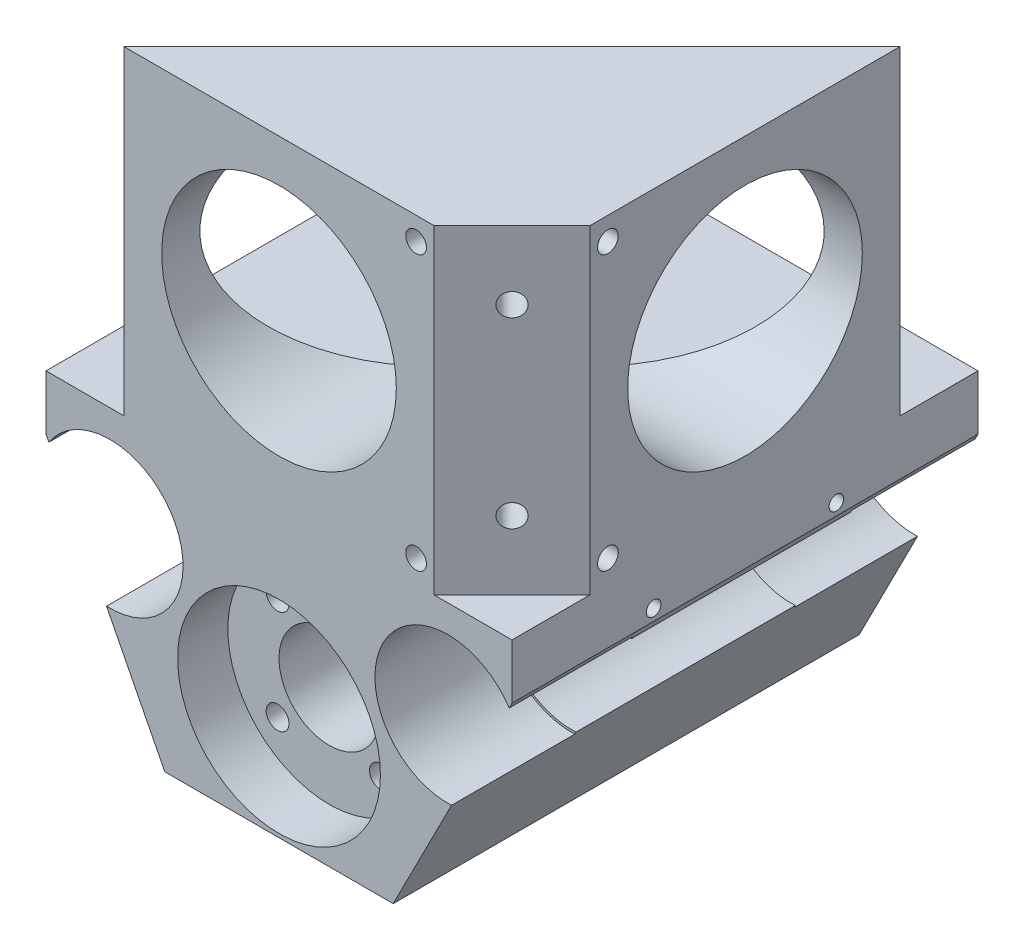
SolidWorks part; units mm, degrees
material "7075-T6 (SN)"
ref_plane "Front Plane" through (0, 0, 0) normal (0, 0, 1) x (1, 0, 0)
ref_plane "Top Plane" through (0, 0, 0) normal (0, 1, 0) x (1, 0, 0)
ref_plane "Right Plane" through (0, 0, 0) normal (1, 0, 0) x (0, 0, -1)
sketch "Sketch1" plane through (0, 0, 0) normal (0, 0, 1) x (1, 0, 0)
  line L0 (-25.5, 0) -> (25.5, 0)
  line L1 (-25.5, 0) -> (-25.5, -6)
  line L2 (-25.5, -6) -> (-12.5, -31.5)
  line L3 (-12.5, -31.5) -> (12.5, -31.5)
  line L4 (12.5, -31.5) -> (25.5, -6)
  line L5 (25.5, -6) -> (25.5, 0)
  point P7 (0, -31.5)
  dimension "D1" = 51
  dimension "D2" = 31.5
  dimension "D3" = 25
  dimension "D4" = 6
extrude "Boss-Extrude1" add sketch "Sketch1" along normal blind 51
sketch "Sketch2" plane through (0, 0, 51) normal (0, 0, 1) x (1, 0, 0)
  line L2 (-18.5, -11) -> (18.5, -11) construction
  line L3 (25.5, 0) -> (-25.5, 0) construction
  circle A2 centre (-18.5, -11) radius 7.75
  circle A3 centre (18.5, -11) radius 7.75
  point P4 (0, -11)
  dimension "D1" = 15.5
  dimension "D2" = 37
  dimension "D3" = 11
extrude "Cut-Extrude1" cut sketch "Sketch2" against normal up to next
sketch "Sketch6" plane through (0, 0, 51) normal (0, 0, 1) x (1, 0, 0)
  line L0 (-12.5, -31.5) -> (12.5, -31.5) construction
  circle A0 centre (0, -20) radius 5.5
  dimension "D1" = 11
  dimension "D2" = 11.5
extrude "Cut-Extrude2" cut sketch "Sketch6" against normal up to next
hole_wizard "M3 Tapped Hole2" positions "Sketch7" profile "Sketch8" tap size "M3" standard "DIN"
sketch "Sketch7" plane through (0, 0, 51) normal (0, 0, 1) x (1, 0, 0)
  line L0 (5.6569, -14.3431) -> (-5.6569, -25.6569) construction
  line L2 (-5.6569, -14.3431) -> (5.6569, -25.6569) construction
  circle A2 centre (0, -20) radius 5.5 construction
  point P0 (-5.6569, -14.3431)
  point P2 (5.6569, -25.6569)
  point P4 (5.6569, -14.3431)
  point P6 (-5.6569, -25.6569)
  point P25 (0, -20)
  point P26 (0, -20)
  dimension "D1" = 16
sketch "Sketch8" plane through (-5.6569, -14.3431, 51) normal (1, 0, 0) x (0, -1, 0)
  line L0 (0, 0) -> (0, 12.2511)
  line L1 (0, 12.2511) -> (1.25, 11.5)
  line L2 (1.25, 11.5) -> (1.25, 0)
  line L5 (1.25, 0) -> (0, 0)
  line L10 (0, 12.2511) -> (-1.25, 11.5) construction
  line L11 (0, -6.35) -> (0, 107.95) construction
  dimension "Tap Drill Dia." = 2.5
  dimension "Tap Drill Depth" = 11.5
  dimension "Drill Angle" = 118
cosmetic thread "Hole Thread5" parameters "D1"=10, "D2"=3
cosmetic thread "Hole Thread6" parameters "D1"=10, "D2"=3
cosmetic thread "Hole Thread7" parameters "D1"=10, "D2"=3
cosmetic thread "Hole Thread8" parameters "D1"=10, "D2"=3
sketch "Sketch13" plane through (0, 0, 0) normal (0, 0, -1) x (-1, 0, 0)
  circle A0 centre (0, -20) radius 10.5
  circle A1 centre (0, -20) radius 5.5 construction
  dimension "D1" = 21
extrude "Cut-Extrude5" cut sketch "Sketch13" against normal blind 15
sketch "Sketch22" plane through (0, 0, 0) normal (0, 1, 0) x (1, 0, 0)
  line L4 (25.5, -51) -> (25.5, 0) construction
  line L5 (-25.4558, -42.4706) -> (-16.9706, -50.9558) construction
  line L6 (-16.9706, -50.9558) -> (25.4558, -8.5294) construction
  line L7 (25.4558, -8.5294) -> (16.9706, -0.0442) construction
  line L8 (16.9706, -0.0442) -> (-25.4558, -42.4706) construction
  line L9 (-21.2132, -46.7132) -> (21.2132, -4.2868) construction
  line L34 (25.5, -51) -> (-25.5, -51) construction
  line L37 (16.9706, -51) -> (25.5, -51) construction
  line L38 (25.5, -51) -> (25.5, -42.4706) construction
  line L39 (-16.9706, -50.9558) -> (-16.9706, -51)
  line L40 (-16.9706, -51) -> (16.9706, -51)
  line L41 (16.9706, -51) -> (25.5, -42.4706)
  line L42 (25.5, -42.4706) -> (25.5, -8.5294)
  line L43 (25.5, -8.5294) -> (25.4558, -8.5294)
  line L44 (25.4558, -8.5294) -> (-16.9706, -50.9558)
  line L45 (-25.5, -51) -> (-16.9706, -51) construction
  point P7 (25.5, -25.5)
  point P10 (0, -25.5)
  dimension "D1" = 60
  dimension "D2" = 12
  dimension "D3" = 45
extrude "Boss-Extrude2" add sketch "Sketch22" along normal blind 35
sketch "Sketch24" plane through (0, 0, 51) normal (0, 0, 1) x (1, 0, 0)
  line L0 (-16.9706, 35) -> (-16.9706, 0) construction
  circle A0 centre (0, 17.5) radius 12.8397
  point P7 (-16.9706, 17.5)
  dimension "D1" = 25.6794
extrude "Cut-Extrude6" cut sketch "Sketch24" against normal up to next
cosmetic thread "Cosmetic Thread2" parameters "D2"=26.289
sketch "Sketch25" plane through (25.5, 0, 0) normal (1, 0, 0) x (0, 0, -1)
  line L0 (-42.4706, 35) -> (-8.5294, 35) construction
  line L1 (-8.5294, 35) -> (-8.5294, 0) construction
  circle A0 centre (-25.5, 17.5) radius 12.8397
  point P5 (-25.5, 35)
  point P9 (-8.5294, 17.5)
  dimension "D1" = 25.6794
extrude "Cut-Extrude7" cut sketch "Sketch25" against normal up to next
cosmetic thread "Cosmetic Thread3" parameters "D2"=26.289
hole_wizard "M2 Tapped Hole1" positions "Sketch26" profile "Sketch27" tap size "M2" standard "DIN"
sketch "Sketch26" plane through (16.9926, 0, 16.9926) normal (-0.7071, 0, -0.7071) x (-0.7071, 0, 0.7071)
  line L1 (-6.9688, 5.5) -> (43.0312, 5.5) construction
  line L2 (-6.9688, 5.5) -> (-6.9688, 29.5) construction
  line L3 (-6.9688, 29.5) -> (43.0312, 29.5) construction
  line L4 (43.0312, 5.5) -> (43.0312, 29.5) construction
  line L5 (-6.9688, 5.5) -> (43.0312, 29.5) construction
  line L6 (-6.9688, 29.5) -> (43.0312, 5.5) construction
  line L7 (18.0312, 5.3815) -> (18.0312, 29.6185) construction
  point P2 (43.0312, 29.5)
  point P103 (-6.9688, 5.5)
  point P104 (-6.9688, 29.5)
  point P105 (43.0312, 5.5)
  point P110 (18.0312, 17.5)
  dimension "D1" = 24
  dimension "D2" = 50
cosmetic thread "Hole Thread9" parameters "D1"=2, "D2"=2
cosmetic thread "Hole Thread10" parameters "D1"=2, "D2"=2
cosmetic thread "Hole Thread11" parameters "D1"=2, "D2"=2
cosmetic thread "Hole Thread12" parameters "D1"=2, "D2"=2
sketch "Sketch27" plane through (-13.435, 29.5, 47.4203) normal (0, 1, 0) x (-0.7071, 0, 0.7071)
  line L0 (0, 0) -> (0, 3.6807)
  line L1 (0, 3.6807) -> (0.8, 3.2)
  line L2 (0.8, 3.2) -> (0.8, 0)
  line L5 (0.8, 0) -> (0, 0)
  line L10 (0, 3.6807) -> (-0.8, 3.2) construction
  line L11 (0, -6.35) -> (0, 107.95) construction
  dimension "Tap Drill Dia." = 1.6
  dimension "Tap Drill Depth" = 3.2
  dimension "Drill Angle" = 118
hole_wizard "M3 Tapped Hole4" positions "Sketch34" profile "Sketch33" tap size "M3" standard "DIN"
sketch "Sketch34" plane through (33.9853, 0, 33.9853) normal (0.7071, 0, 0.7071) x (0.7071, 0, -0.7071)
  line L0 (-24.0624, 35) -> (-12, 35) construction
  point P0 (-18.0312, 27.5)
  point P2 (-18.0312, 7.5)
  point P8 (-18.0312, 35)
  dimension "D1" = 20
  dimension "D2" = 7.5
sketch "Sketch33" plane through (21.2353, 27.5, 46.7353) normal (0, 1, 0) x (0.7071, 0, -0.7071)
  line L0 (0, 0) -> (0, 8.2511)
  line L1 (0, 8.2511) -> (1.25, 7.5)
  line L2 (1.25, 7.5) -> (1.25, 0)
  line L5 (1.25, 0) -> (0, 0)
  line L10 (0, 8.2511) -> (-1.25, 7.5) construction
  line L11 (0, -6.35) -> (0, 107.95) construction
  dimension "Tap Drill Dia." = 2.5
  dimension "Tap Drill Depth" = 7.5
  dimension "Drill Angle" = 118
cosmetic thread "Hole Thread21" parameters "D1"=6, "D2"=3
cosmetic thread "Hole Thread22" parameters "D1"=6, "D2"=3
hole_wizard "M2 Tapped Hole2" positions "Sketch35" profile "Sketch36" tap size "M2" standard "DIN"
sketch "Sketch35" plane through (25.5, 0, 0) normal (1, 0, 0) x (0, 0, -1)
  line L0 (-51, -6) -> (0, -6) construction
  point P0 (-35.5, -4.75)
  point P2 (-15.5, -4.75)
  point P7 (-25.5, -6)
  dimension "D1" = 10
  dimension "D2" = 20
  dimension "D3" = 1.25
sketch "Sketch36" plane through (25.5, -4.75, 35.5) normal (0, 1, 0) x (0, 0, -1)
  line L0 (0, 0) -> (0, 7.6807)
  line L1 (0, 7.6807) -> (0.8, 7.2)
  line L2 (0.8, 7.2) -> (0.8, 0)
  line L5 (0.8, 0) -> (0, 0)
  line L10 (0, 7.6807) -> (-0.8, 7.2) construction
  line L11 (0, -6.35) -> (0, 107.95) construction
  dimension "Tap Drill Dia." = 1.6
  dimension "Tap Drill Depth" = 7.2
  dimension "Drill Angle" = 118
cosmetic thread "Hole Thread23" parameters "D1"=6, "D2"=2
cosmetic thread "Hole Thread24" parameters "D1"=6, "D2"=2
mirror "Mirror1" about plane through (0, 0, 0) normal (1, 0, 0) of "M2 Tapped Hole2"
sketch "Sketch38" plane through (0, 0, 51) normal (0, 0, 1) x (1, 0, 0)
  circle A0 centre (0, -20) radius 11.1
  dimension "D1" = 22.2
extrude "Cut-Extrude8" cut sketch "Sketch38" against normal blind 5.5
sketch "Sketch39" plane through (0, 0, 0) normal (0, 0, -1) x (-1, 0, 0)
  circle A0 centre (18.5, -11) radius 8
  circle A1 centre (-18.5, -11) radius 8
  dimension "D1" = 16
extrude "Cut-Extrude9" cut sketch "Sketch39" against normal blind 13.5
sketch "Sketch41" plane through (0, 0, 51) normal (0, 0, 1) x (1, 0, 0)
  circle A0 centre (18.5, -11) radius 8
  circle A1 centre (-18.5, -11) radius 8
  dimension "D1" = 16
extrude "Cut-Extrude10" cut sketch "Sketch41" against normal blind 13.5
hole_wizard "#4-40 Tapped Hole1" positions "Sketch43" profile "Sketch44" tap size "#4-40" standard "ANSI Inch"
sketch "Sketch43" plane through (25.5, 0, 0) normal (1, 0, 0) x (0, 0, -1)
  line L1 (-40.5, 2.5) -> (-10.5, 2.5) construction
  line L2 (-40.5, 2.5) -> (-40.5, 32.5) construction
  line L3 (-40.5, 32.5) -> (-10.5, 32.5) construction
  line L4 (-10.5, 2.5) -> (-10.5, 32.5) construction
  line L5 (-40.5, 2.5) -> (-10.5, 32.5) construction
  line L6 (-40.5, 32.5) -> (-10.5, 2.5) construction
  line L7 (-42.4706, 35) -> (-8.5294, 35) construction
  line L8 (-8.5294, 35) -> (-8.5294, 0) construction
  point P129 (-40.5, 2.5)
  point P130 (-40.5, 32.5)
  dimension "D1" = 30
  dimension "D2" = 2.5
  dimension "D3" = 1.9706
sketch "Sketch44" plane through (25.5, 32.5, 40.5) normal (0, 1, 0) x (0, 0, -1)
  line L0 (0, 0) -> (0, 8.2692)
  line L1 (0, 8.2692) -> (1.1303, 7.59)
  line L2 (1.1303, 7.59) -> (1.1303, 0)
  line L5 (1.1303, 0) -> (0, 0)
  line L10 (0, 8.2692) -> (-1.1303, 7.59) construction
  line L11 (0, -6.35) -> (0, 107.95) construction
  dimension "Tap Drill Dia." = 2.2606
  dimension "Tap Drill Depth" = 7.59
  dimension "Drill Angle" = 118
cosmetic thread "Hole Thread25" parameters "D1"=5.69, "D2"=2.8448
cosmetic thread "Hole Thread26" parameters "D1"=5.69, "D2"=2.8448
hole_wizard "#4-40 Tapped Hole2" positions "Sketch45" profile "Sketch46" tap size "#4-40" standard "ANSI Inch"
sketch "Sketch45" plane through (0, 0, 51) normal (0, 0, 1) x (1, 0, 0)
  circle A0 centre (0, 17.5) radius 12.8397 construction
  point P0 (15, 32.5)
  point P2 (15, 2.5)
  point P7 (0, 0)
  dimension "D1" = 15
  dimension "D2" = 15
  dimension "D3" = 15
sketch "Sketch46" plane through (15, 32.5, 51) normal (1, 0, 0) x (0, -1, 0)
  line L0 (0, 0) -> (0, 8.2792)
  line L1 (0, 8.2792) -> (1.1303, 7.6)
  line L2 (1.1303, 7.6) -> (1.1303, 0)
  line L5 (1.1303, 0) -> (0, 0)
  line L10 (0, 8.2792) -> (-1.1303, 7.6) construction
  line L11 (0, -6.35) -> (0, 107.95) construction
  dimension "Tap Drill Dia." = 2.2606
  dimension "Tap Drill Depth" = 7.6
  dimension "Drill Angle" = 118
cosmetic thread "Hole Thread27" parameters "D1"=5.69, "D2"=2.8448
cosmetic thread "Hole Thread28" parameters "D1"=5.69, "D2"=2.8448
